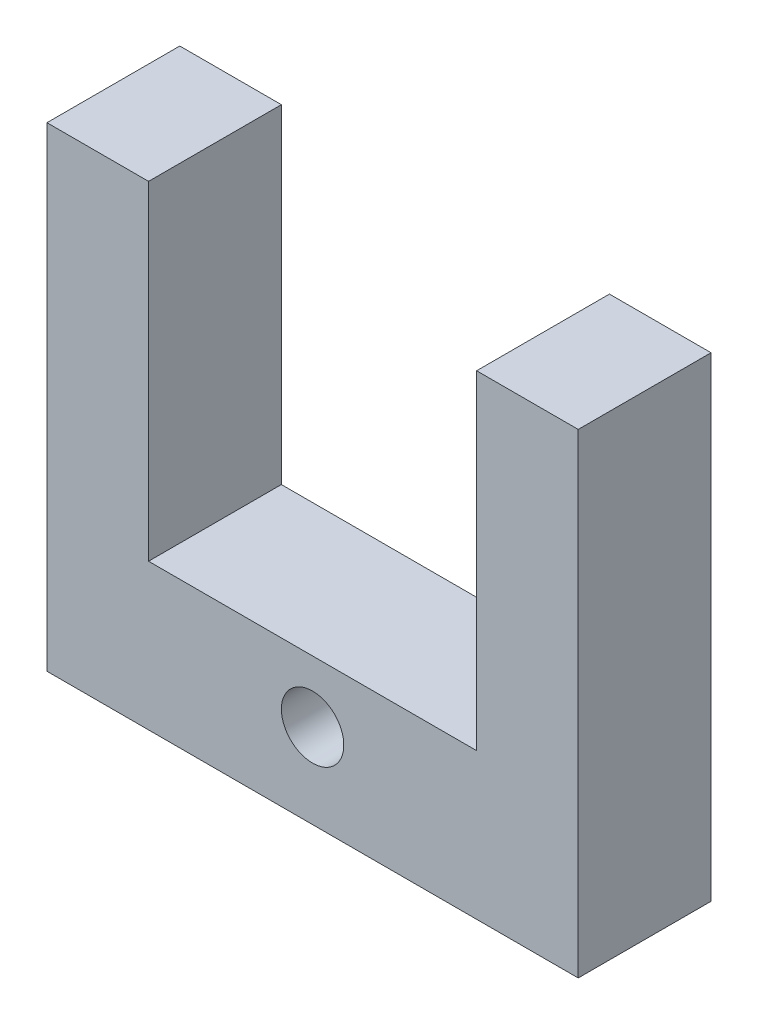
SolidWorks part; units mm, degrees
ref_plane "Front Plane" through (0, 0, 0) normal (0, 0, 1) x (1, 0, 0)
ref_plane "Top Plane" through (0, 0, 0) normal (0, 1, 0) x (1, 0, 0)
ref_plane "Right Plane" through (0, 0, 0) normal (1, 0, 0) x (0, 0, -1)
sketch "Sketch3" plane through (0, 0, 0) normal (0, 0, 1) x (1, 0, 0)
  line L1 (-10, 35) -> (10, 35)
  line L2 (-10, 35) -> (-10, -35)
  line L3 (-10, -35) -> (10, -35)
  line L4 (10, 35) -> (10, -35)
  line L5 (-10, 35) -> (10, -35) construction
  line L6 (-10, -35) -> (10, 35) construction
  point P0 (0, 0)
  dimension "D1" = 20
  dimension "D2" = 70
extrude "Boss-Extrude3" add sketch "Sketch3" along normal blind 5
sketch "Sketch4" plane through (0, 0, 5) normal (0, 0, 1) x (1, 0, 0)
  line L0 (-1.875, 12.7392) -> (1.875, 12.7392)
  line L1 (-2.85, 24.85) -> (2.85, 24.85)
  line L2 (-2.85, 24.85) -> (-1.875, 12.7392)
  line L3 (2.85, 24.85) -> (1.875, 12.7392)
  line L4 (10, -35) -> (10, 35) construction
  line L7 (10, 35) -> (-10, 35) construction
  circle A0 centre (0, 27) radius 3.57
  arc A1 (-1.875, 12.7392) -> (1.875, 12.7392) centre (0, 12.7392) ccw
  dimension "D1" = 7.14
  dimension "D2" = 3.75
  dimension "D3" = 5.7
  dimension "D4" = 12.15
  dimension "D5" = 12.15
  dimension "D6" = 10
  dimension "D7" = 8
extrude "Cut-Extrude2" cut sketch "Sketch4" against normal blind 2 contours L0 A1 | A0 L2 L0 L3
sketch "Sketch6" plane through (0, 0, 3) normal (0, 0, 1) x (1, 0, 0)
  line L0 (10, 35) -> (-10, 35) construction
  line L1 (-10, 35) -> (-10, -35) construction
  circle A0 centre (0, 27) radius 3.57
  dimension "D1" = 7.14
  dimension "D2" = 8
  dimension "D3" = 10
extrude "Cut-Extrude3" cut sketch "Sketch6" against normal blind 3
sketch "Sketch7" plane through (0, 0, 5) normal (0, 0, 1) x (1, 0, 0)
  line L0 (10, -35) -> (10, 35) construction
  line L1 (-6.175, -6.5) -> (6.175, -6.5)
  line L2 (-6.175, -6.5) -> (-6.175, -29.5)
  line L3 (-6.175, -29.5) -> (6.175, -29.5)
  line L4 (6.175, -6.5) -> (6.175, -29.5)
  line L5 (-6.175, -6.5) -> (6.175, -29.5) construction
  line L6 (-6.175, -29.5) -> (6.175, -6.5) construction
  line L7 (-10, -35) -> (10, -35) construction
  line L8 (0, -18) -> (16.5777, -18) construction
  circle A0 centre (0, -4.18) radius 1.175
  circle A1 centre (0, -31.82) radius 1.175
  point P0 (0, -18)
  dimension "D6" = 2.35
  dimension "D1" = 12.35
  dimension "D2" = 23
  dimension "D3" = 10
  dimension "D4" = 17
  dimension "D5" = 10
  dimension "D7" = 2.32
extrude "Cut-Extrude4" cut sketch "Sketch7" against normal blind 5
sketch "Sketch8" plane through (10, 0, 0) normal (1, 0, 0) x (0, 0, -1)
  line L6 (0, 35) -> (-1.25, 35)
  line L7 (0, 35) -> (0, 10)
  line L8 (0, 10) -> (-1.25, 10)
  line L9 (-1.25, 35) -> (-1.25, 10)
  dimension "D1" = 25
  dimension "D2" = 1.25
extrude "Cut-Extrude5" cut sketch "Sketch8" against normal blind 30
sketch "Sketch10" plane through (0, 0, 5) normal (0, 0, 1) x (1, 0, 0)
  line L0 (-10, 35) -> (-10, -35) construction
  line L1 (-10, -17.1147) -> (10, -17.1147)
  line L2 (-10, -17.1147) -> (-10, -35)
  line L3 (-10, -35) -> (10, -35)
  line L4 (10, -17.1147) -> (10, -35)
  line L6 (-10, -17.1147) -> (10, -17.1147)
  line L7 (-10, -17.1147) -> (-10, 35)
  line L8 (-10, 35) -> (10, 35)
  line L9 (10, -17.1147) -> (10, 35)
  circle M6 centre (0, -4.18) radius 1.175
  line M7 (6.175, -6.5) -> (6.175, -29.5)
  line M9 (-6.175, -29.5) -> (-6.175, -6.5)
  line M10 (-6.175, -6.5) -> (6.175, -6.5)
  arc M11 (1.875, 12.7392) -> (-1.875, 12.7392) centre (0, 12.7392) cw
  line M12 (-1.875, 12.7392) -> (-2.85, 24.85)
  arc M13 (-2.85, 24.85) -> (2.85, 24.85) centre (0, 27) cw
  line M14 (2.85, 24.85) -> (1.875, 12.7392)
  line M15 (10, -35) -> (10, 35)
  line M16 (10, 35) -> (-10, 35)
  line M17 (-10, 35) -> (-10, -35)
extrude "Cut-Extrude8" cut sketch "Sketch10" against normal blind 10 contours L1 M17 M9 M10 M7 M15 M16 M14 M11 M12 M13 M6 | M11 M14 M13 M12
